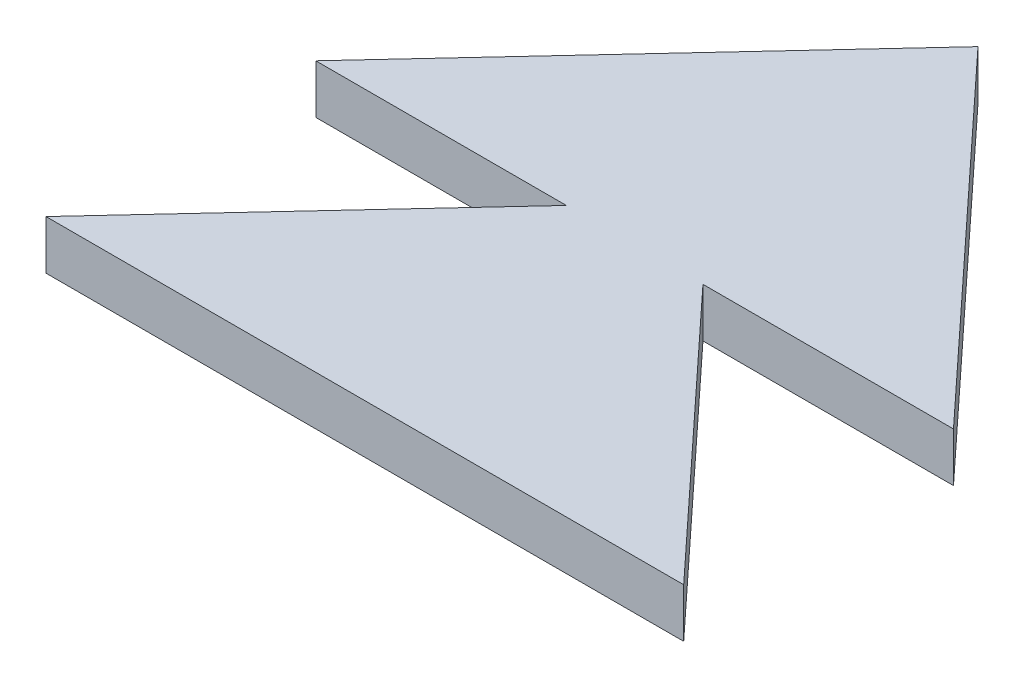
SolidWorks part; units mm, degrees
ref_plane "Front Plane" through (0, 0, 0) normal (0, 0, 1) x (1, 0, 0)
ref_plane "Top Plane" through (0, 0, 0) normal (0, 1, 0) x (1, 0, 0)
ref_plane "Right Plane" through (0, 0, 0) normal (1, 0, 0) x (0, 0, -1)
sketch "Sketch2" plane through (0, 0, 0) normal (0, 1, 0) x (1, 0, 0)
  line L0 (0, 0) -> (13, 0)
  line L1 (13, 0) -> (7.8929, 5.5)
  line L2 (5.1071, 5.5) -> (0, 0)
  line L3 (6.5, 0) -> (6.5, 7) construction
  line L5 (13, 5.5) -> (6.5, 12.5)
  line L6 (6.5, 12.5) -> (0, 5.5)
  line L8 (0, 5.5) -> (5.1071, 5.5)
  line L9 (6.5, 5.5) -> (6.5, 12.5) construction
  line L10 (7.8929, 5.5) -> (13, 5.5)
  point P7 (0, 0)
  dimension "D1" = 7
  dimension "D2" = 13
  dimension "D3" = 13
  dimension "D4" = 7
  dimension "D5" = 5.5
extrude "Boss-Extrude2" add sketch "Sketch2" along normal blind 1
